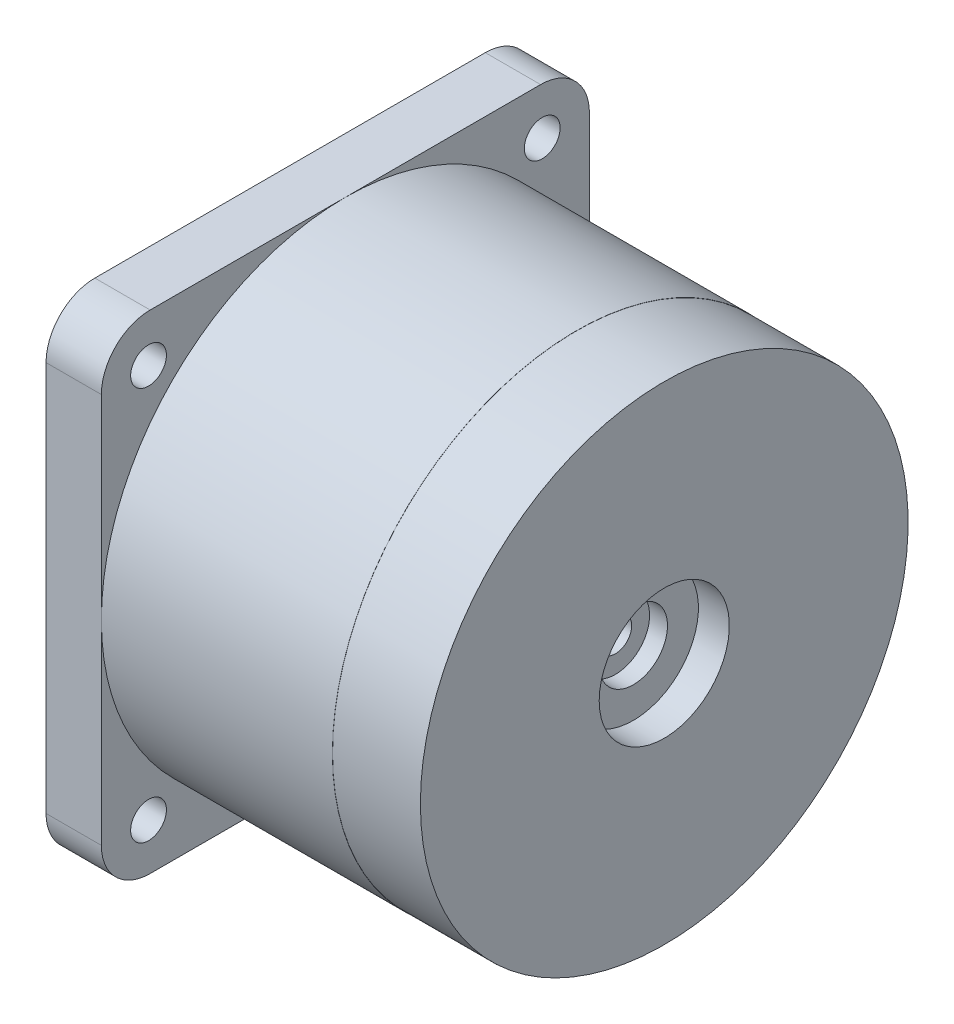
SolidWorks part; units mm, degrees
ref_plane "Plan de face" through (0, 0, 0) normal (0, 0, 1) x (1, 0, 0)
ref_plane "Plan de dessus" through (0, 0, 0) normal (0, 1, 0) x (1, 0, 0)
ref_plane "Plan de droite" through (0, 0, 0) normal (1, 0, 0) x (0, 0, -1)
sketch "Esquisse1" plane through (0, 0, 0) normal (0, 0, 1) x (1, 0, 0)
  line L0 (0, 0) -> (49.68, 0) construction
  line L1 (0, 0) -> (0, 14.99)
  line L2 (0, 14.99) -> (-5.4, 14.99)
  line L3 (-5.4, 14.99) -> (-5.4, 15)
  line L4 (-5.4, 15) -> (-19.6, 15)
  line L5 (-19.6, 15) -> (-19.6, 0)
  line L6 (-19.6, 0) -> (0, 0)
  dimension "D1" = 30
  dimension "D2" = 29.98
  dimension "D3" = 5.4
  dimension "D4" = 19.6
revolve "Révolution1" add sketch "Esquisse1" angle 360 about L0
sketch "Esquisse2" plane through (-19.6, 0, 0) normal (-1, 0, 0) x (0, 0, 1)
  line L0 (-12.1, 12.1) -> (12.1, 12.1) construction
  line L1 (-15, 15) -> (15, 15)
  line L2 (-15, 15) -> (-15, -15)
  line L3 (-15, -15) -> (15, -15)
  line L4 (15, 15) -> (15, -15)
  line L5 (12.1, 12.1) -> (12.1, -12.1) construction
  line L6 (-12.1, -12.1) -> (12.1, -12.1) construction
  line L7 (-12.1, 12.1) -> (-12.1, -12.1) construction
  circle A0 centre (-12.1, 12.1) radius 1.1
  circle A1 centre (12.1, 12.1) radius 1.1
  circle A2 centre (-12.1, -12.1) radius 1.1
  circle A3 centre (12.1, -12.1) radius 1.1
  dimension "D6" = 2.2
  dimension "D2" = 30
  dimension "D3" = 15
  dimension "D4" = 15
  dimension "D1" = 24.2
  dimension "D5" = 30
extrude "Extrusion1" add sketch "Esquisse2" along normal blind 3.4
sketch "Esquisse3" plane through (-23, 0, 0) normal (-1, 0, 0) x (0, 0, 1)
  circle A0 centre (0, 0) radius 13.5
  dimension "D1" = 27
extrude "Enlèv. mat.-Extru.1" cut sketch "Esquisse3" against normal blind 1.6
fillet "Congé1" radius 3 4 edges at (-21.3, 15, 15) (-21.3, -15, 15) (-21.3, -15, -15) (-21.3, 15, -15)
sketch "Esquisse4" plane through (-21.4, 0, 0) normal (-1, 0, 0) x (0, 0, 1)
  line L0 (0, 0) -> (0, -4.9) construction
  circle A0 centre (0, -4.9) radius 5
  dimension "D2" = 10
  dimension "D1" = 4.9
extrude "Extrusion2" add sketch "Esquisse4" along normal blind 7.55
sketch "Esquisse5" plane through (0, 0, 0) normal (0, 0, 1) x (1, 0, 0)
  line L0 (0, 0) -> (0, 4)
  line L1 (0, 4) -> (-1.9, 4)
  line L2 (-1.9, 4) -> (-1.9, 2.1)
  line L3 (-1.9, 2.1) -> (-3, 2.1)
  line L4 (-3, 2.1) -> (-3, 1)
  line L5 (-3, 1) -> (-11.5, 1)
  line L6 (-11.5, 1) -> (-11.5, 0)
  line L7 (-11.5, 0) -> (0, 0)
  line L8 (0, 0) -> (6.4969, 0) construction
  dimension "D1" = 3
  dimension "D2" = 1.1
  dimension "D3" = 8.5
  dimension "D4" = 2
  dimension "D5" = 4.2
  dimension "D6" = 8
revolve "Enlèvement de matière-Révolution1" cut sketch "Esquisse5" angle 360 about L8
